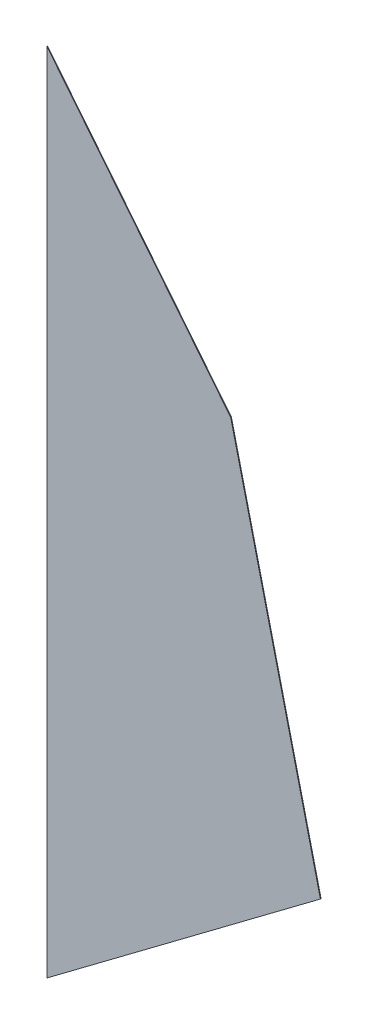
SolidWorks part; units mm, degrees
ref_plane "Front Plane" through (0, 0, 0) normal (0, 0, 1) x (1, 0, 0)
ref_plane "Top Plane" through (0, 0, 0) normal (0, 1, 0) x (1, 0, 0)
ref_plane "Right Plane" through (0, 0, 0) normal (1, 0, 0) x (0, 0, -1)
sketch "Sketch1" plane through (0, 0, 0) normal (0, 0, 1) x (1, 0, 0)
  line L0 (0, 0) -> (1016, 762)
  line L1 (1016, 762) -> (682.945, 2144.858)
  line L2 (682.945, 2144.858) -> (0, 2997.2)
  line L3 (0, 2997.2) -> (0, 0)
  dimension "D1" = 2997.2
  dimension "D2" = 1270
  dimension "D3" = 1016
  dimension "D4" = 1422.4
  dimension "D5" = 1092.2
extrude "Boss-Extrude1" add sketch "Sketch1" along normal blind 2.54
sketch "Sketch2" plane through (0, 0, 2.54) normal (0, 0, 1) x (1, 0, 0)
  line L0 (-204.007, 1579.2614) -> (-640.7565, 66.2363)
  line L1 (-640.7565, 66.2363) -> (-107.6445, 83.7627)
  line L2 (-107.6445, 83.7627) -> (-204.007, 1579.2614)
  line L3 (-204.007, 1579.2614) -> (0, 2286) construction
  line L4 (0, 2997.2) -> (0, 0) construction
  line L5 (-640.7565, 66.2363) -> (-711.2, -177.8) construction
  dimension "D1" = 533.4
  dimension "D2" = 1498.6
  dimension "D3" = 1574.8
  dimension "D4" = 2286
  dimension "D5" = 711.2
  dimension "D6" = 177.8
  dimension "D7" = 254
extrude "Boss-Extrude2" [suppressed] add sketch "Sketch2" against normal blind 2.54 separate body
sketch "Sketch3" [suppressed] plane through (0, 0, 0) normal (0, 1, 0) x (1, 0, 0)
  line L0 (0, 0) -> (268.6252, 71.9779)
  line L2 (682.945, 0) -> (0, 0) construction
  point P3 (271.8336, 58.7094)
  dimension "D1" = 15
ref_plane "Plane1" [suppressed] through (0, 0, 0) normal (-0.9659, 0, 0.2588) x (0.2588, 0, 0.9659)
sketch "Sketch4" [suppressed] plane through (0, 0, 0) normal (-0.9659, 0, 0.2588) x (0.2588, 0, 0.9659)
  line L4 (2.4535, 2997.2) -> (2.4535, 0)
  line L5 (2.4535, 0) -> (265.4136, 762)
  line L6 (265.4136, 762) -> (179.2126, 2144.858)
  line L7 (179.2126, 2144.858) -> (2.4535, 2997.2)
  line L8 (2.4535, 2997.2) -> (2.4535, 0)
  line L9 (2.4535, 0) -> (265.4136, 762)
  line L10 (265.4136, 762) -> (179.2126, 2144.858)
  line L11 (179.2126, 2144.858) -> (2.4535, 2997.2)
  dimension "D1" = 0
extrude "Boss-Extrude3" [suppressed] add sketch "Sketch4" along normal blind 2.54
